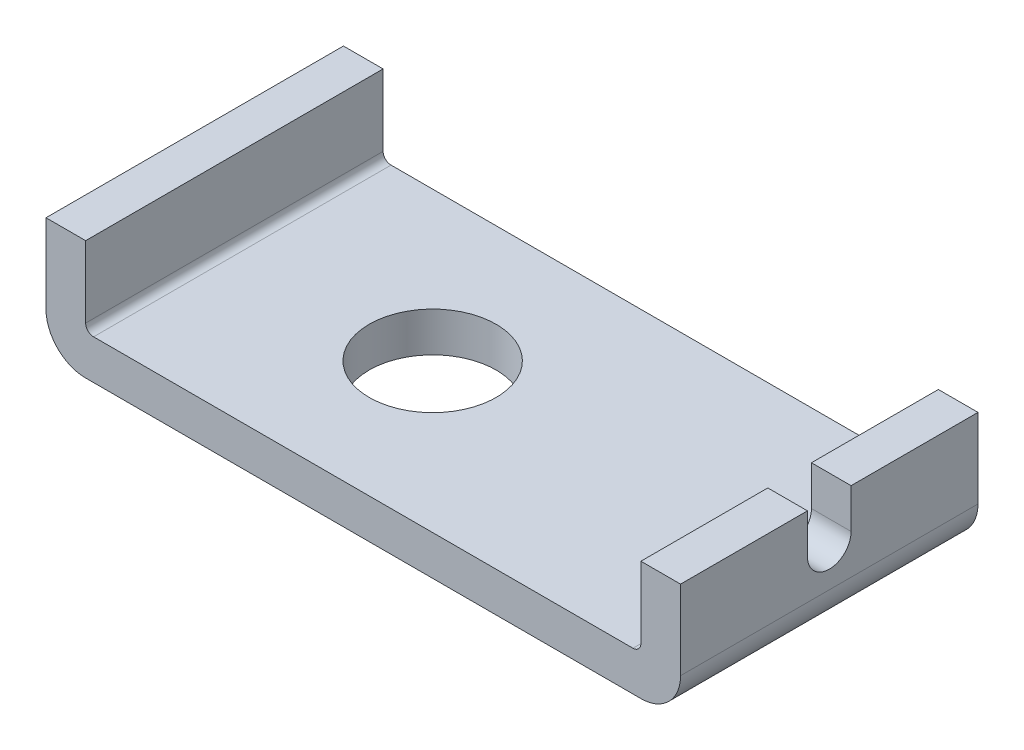
SolidWorks part; units mm, degrees
material "Gray Cast Iron"
ref_plane "Front Plane" through (0, 0, 0) normal (0, 0, 1) x (1, 0, 0)
ref_plane "Top Plane" through (0, 0, 0) normal (0, 1, 0) x (1, 0, 0)
ref_plane "Right Plane" through (0, 0, 0) normal (1, 0, 0) x (0, 0, -1)
sketch "Sketch1" plane through (0, 0, 0) normal (0, 0, 1) x (1, 0, 0)
  line L0 (-91.5167, 34.7558) -> (-81.5167, 34.7558) construction
  line L1 (-91.5167, 34.7558) -> (-81.5167, 34.7558)
  line L2 (-91.5167, 34.7558) -> (-91.5167, 14.7558)
  line L3 (-81.5167, 4.7558) -> (58.4833, 4.7558)
  line L4 (68.4833, 34.7558) -> (68.4833, 14.7558)
  line L5 (68.4833, 34.7558) -> (58.4833, 34.7558) construction
  line L6 (58.4833, 34.7558) -> (68.4833, 34.7558)
  line L8 (-81.5167, 34.7558) -> (-81.5167, 16.7558)
  line L9 (-79.5167, 14.7558) -> (56.4833, 14.7558)
  line L10 (58.4833, 34.7558) -> (58.4833, 16.7558)
  arc A0 (68.4833, 14.7558) -> (58.4833, 4.7558) centre (58.4833, 14.7558) cw
  arc A1 (-81.5167, 4.7558) -> (-91.5167, 14.7558) centre (-81.5167, 14.7558) cw
  arc A2 (56.4833, 14.7558) -> (58.4833, 16.7558) centre (56.4833, 16.7558) ccw
  arc A3 (-79.5167, 14.7558) -> (-81.5167, 16.7558) centre (-79.5167, 16.7558) cw
  point P6 (68.4833, 4.7558)
  dimension "D3" = 10
  dimension "D4" = 2
  dimension "D1" = 160
  dimension "D2" = 30
extrude "Boss-Extrude1" add sketch "Sketch1" against normal mid plane 75
sketch "Sketch2" plane through (68.4833, 0, 0) normal (1, 0, 0) x (0, 0, -1)
  line L0 (37.5, 34.7558) -> (-37.5, 34.7558) construction
  line L1 (0, 34.7558) -> (0, 24.7558) construction
  line L2 (37.5, 14.7558) -> (37.5, 34.7558) construction
  line L5 (-5.5, 24.7558) -> (-5.5, 34.7558)
  line L6 (-5.5, 34.7558) -> (5.5, 34.7558)
  line L7 (5.5, 24.7558) -> (5.5, 34.7558)
  arc A0 (-5.5, 24.7558) -> (5.5, 24.7558) centre (0, 24.7558) ccw
  point P14 (5.5, 24.7558)
  dimension "D3" = 11
  dimension "D1" = 37.5
  dimension "D2" = 10
extrude "Cut-Extrude1" cut sketch "Sketch2" against normal blind 10
sketch "Sketch5" plane through (0, 14.7558, 0) normal (0, 1, 0) x (1, 0, 0)
  line L0 (-91.5167, 37.5) -> (-91.5167, -37.5) construction
  line L1 (56.4833, 37.5) -> (-79.5167, 37.5) construction
  circle A0 centre (-31.5167, 0) radius 16
  dimension "D2" = 32
  dimension "D1" = 37.5
  dimension "60" = 60
extrude "Cut-Extrude4" cut sketch "Sketch5" against normal through all
